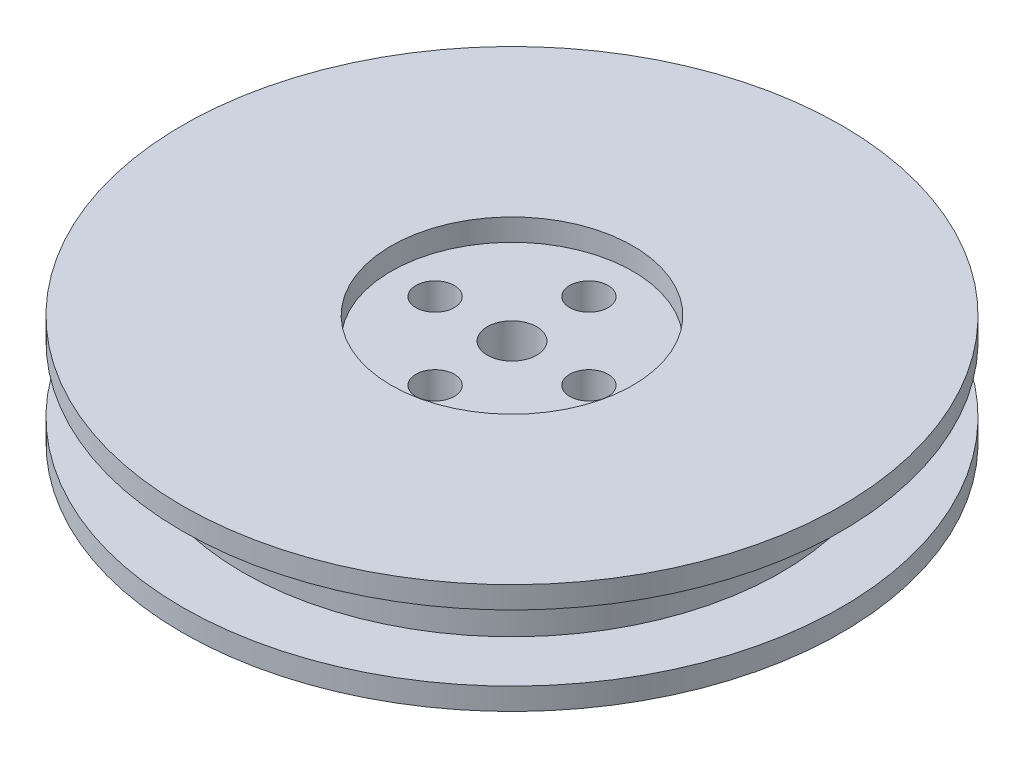
SolidWorks part; units mm, degrees
ref_plane "Front Plane" through (0, 0, 0) normal (0, 0, 1) x (1, 0, 0)
ref_plane "Top Plane" through (0, 0, 0) normal (0, 1, 0) x (1, 0, 0)
ref_plane "Right Plane" through (0, 0, 0) normal (1, 0, 0) x (0, 0, -1)
sketch "Sketch1" plane through (0, 0, 0) normal (0, 1, 0) x (1, 0, 0)
  circle A0 centre (0, 0) radius 30
  dimension "D1" = 60
extrude "Boss-Extrude1" add sketch "Sketch1" along normal blind 2
sketch "Sketch2" plane through (0, 2, 0) normal (0, 1, 0) x (1, 0, 0)
  circle A0 centre (0, 0) radius 24.5
  circle A1 centre (0, 0) radius 30 construction
  dimension "D1" = 5.5
extrude "Boss-Extrude2" add sketch "Sketch2" along normal blind 6
sketch "Sketch3" plane through (0, 8, 0) normal (0, 1, 0) x (1, 0, 0)
  circle A0 centre (0, 0) radius 30
  dimension "D1" = 60
extrude "Boss-Extrude3" add sketch "Sketch3" along normal blind 2
sketch "Sketch4" plane through (0, 10, 0) normal (0, 1, 0) x (1, 0, 0)
  circle A0 centre (0, 0) radius 11
  circle A1 centre (0, 0) radius 2.25
  dimension "D1" = 22
extrude "Cut-Extrude1" cut sketch "Sketch4" against normal blind 2
sketch "Sketch5" plane through (0, 10, 0) normal (0, 1, 0) x (1, 0, 0)
  circle A0 centre (0, 0) radius 2.25
extrude "Cut-Extrude2" cut sketch "Sketch5" against normal blind 27
sketch "Sketch6" plane through (0, 8, 0) normal (0, 1, 0) x (1, 0, 0)
  circle A0 centre (0, 7) radius 1.75
  circle A2 centre (0, 0) radius 2.25 construction
  circle A3 centre (7, 0) radius 1.75
  circle A4 centre (0, -7) radius 1.75
  circle A5 centre (-7, 0) radius 1.75
  point P13 (0, 0)
  dimension "D1" = 7
  dimension "D2" = 4
extrude "Cut-Extrude3" cut sketch "Sketch6" against normal blind 27
sketch "Sketch7" plane through (0, 0, 0) normal (0, -1, 0) x (1, 0, 0)
  circle A0 centre (0, 0) radius 11
extrude "Cut-Extrude4" cut sketch "Sketch7" against normal blind 2
